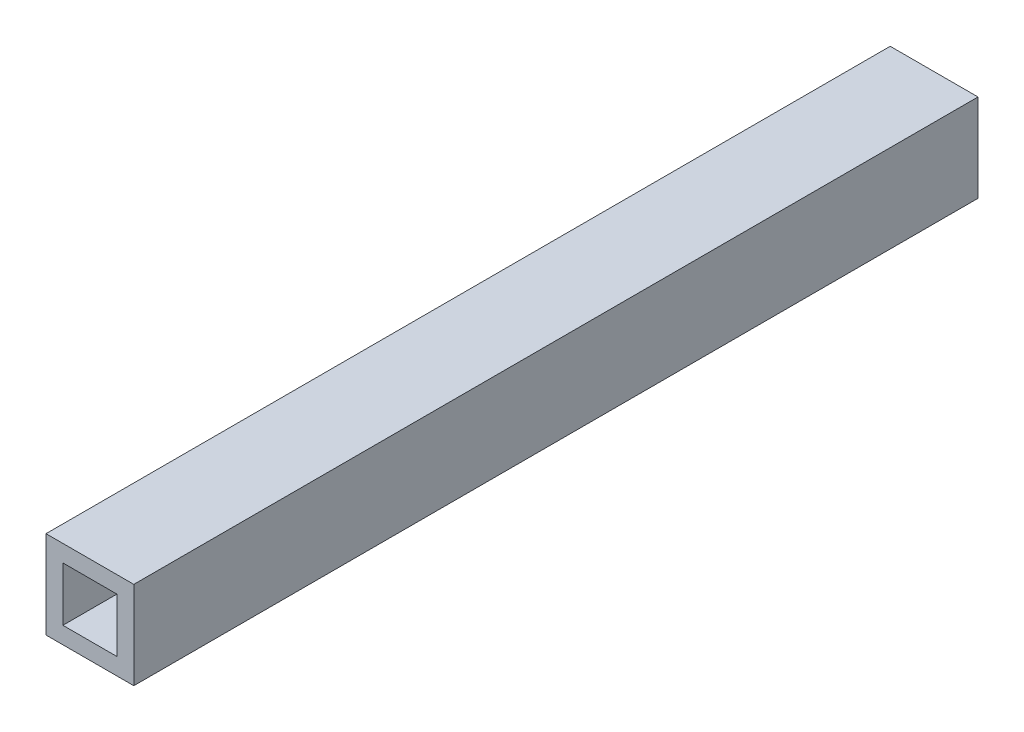
SolidWorks part; units mm, degrees
ref_plane "Front Plane" through (0, 0, 0) normal (0, 0, 1) x (1, 0, 0)
ref_plane "Top Plane" through (0, 0, 0) normal (0, 1, 0) x (1, 0, 0)
ref_plane "Right Plane" through (0, 0, 0) normal (1, 0, 0) x (0, 0, -1)
sketch "Sketch1" plane through (0, 0, 0) normal (0, 0, 1) x (1, 0, 0)
  line L0 (-19.3873, -16.1708) -> (-19.3873, -17.2108)
  line L1 (-19.1873, -16.3708) -> (-18.5473, -16.3708)
  line L2 (-19.1873, -16.3708) -> (-19.1873, -17.0108)
  line L3 (-19.1873, -17.0108) -> (-18.5473, -17.0108)
  line L4 (-18.5473, -16.3708) -> (-18.5473, -17.0108)
  line L5 (-19.1873, -16.3708) -> (-18.5473, -17.0108) construction
  line L6 (-19.1873, -17.0108) -> (-18.5473, -16.3708) construction
  line L7 (-19.3873, -17.2108) -> (-18.3473, -17.2108)
  line L8 (-18.3473, -16.1708) -> (-18.3473, -17.2108)
  line L9 (-19.3873, -16.1708) -> (-18.3473, -16.1708)
  point P0 (-18.8673, -16.6908)
  dimension "D1" = 0.2
extrude "Boss-Extrude1" add sketch "Sketch1" along normal blind 10
